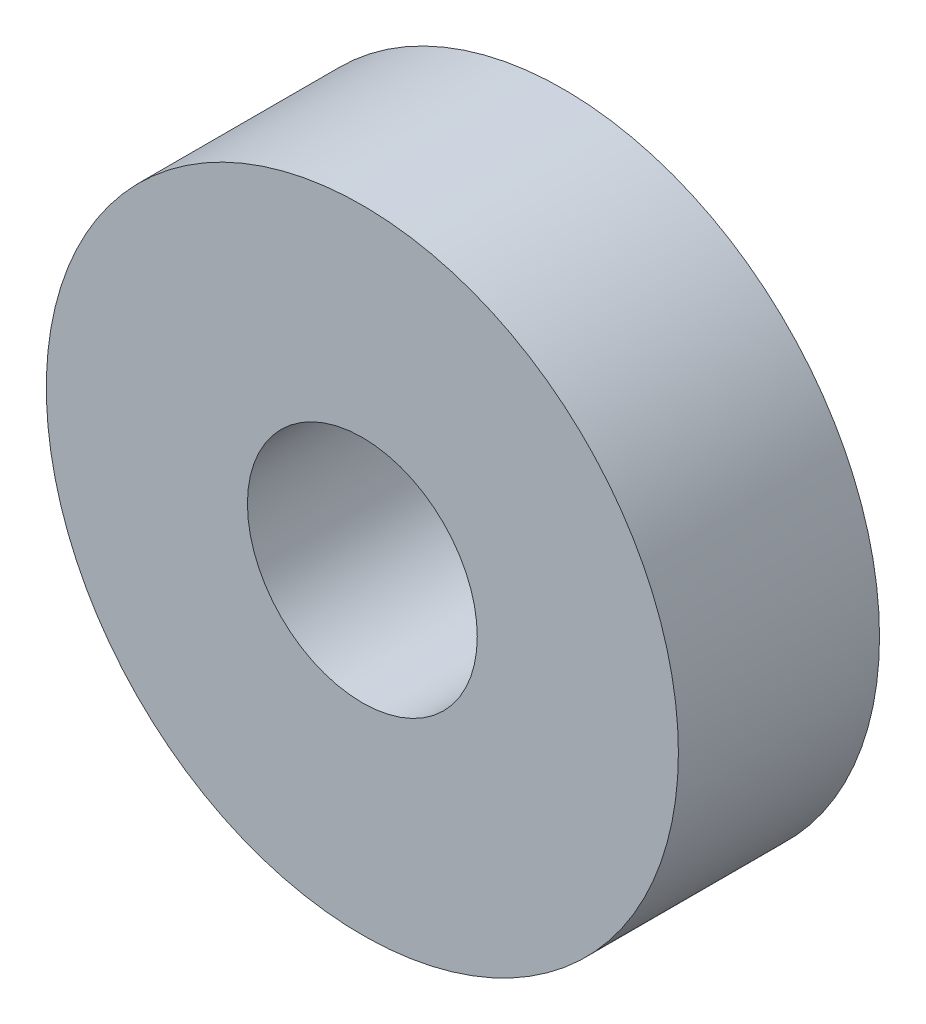
SolidWorks part; units mm, degrees
material "Plain Carbon Steel"
ref_plane "Front Plane" through (0, 0, 0) normal (0, 0, 1) x (1, 0, 0)
ref_plane "Top Plane" through (0, 0, 0) normal (0, 1, 0) x (1, 0, 0)
ref_plane "Right Plane" through (0, 0, 0) normal (1, 0, 0) x (0, 0, -1)
sketch "Sketch2" plane through (0, 0, 0) normal (0, 0, 1) x (1, 0, 0)
  circle A0 centre (0, 0) radius 11
  circle A1 centre (0, 0) radius 4
extrude "Boss-Extrude1" add sketch "Sketch2" along normal blind 7
